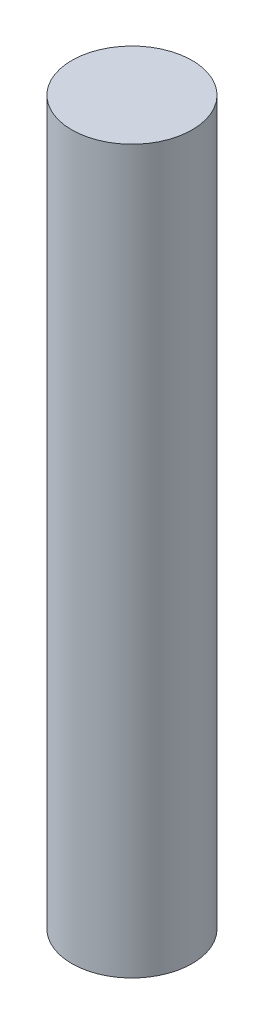
SolidWorks part; units mm, degrees
ref_plane "Front Plane" through (0, 0, 0) normal (0, 0, 1) x (1, 0, 0)
ref_plane "Top Plane" through (0, 0, 0) normal (0, 1, 0) x (1, 0, 0)
ref_plane "Right Plane" through (0, 0, 0) normal (1, 0, 0) x (0, 0, -1)
sketch "Sketch1" plane through (0, 0, 0) normal (0, 1, 0) x (1, 0, 0)
  circle A0 centre (0, 0) radius 12.7
  dimension "D1" = 25.4
extrude "Boss-Extrude1" add sketch "Sketch1" along normal blind 152.4
